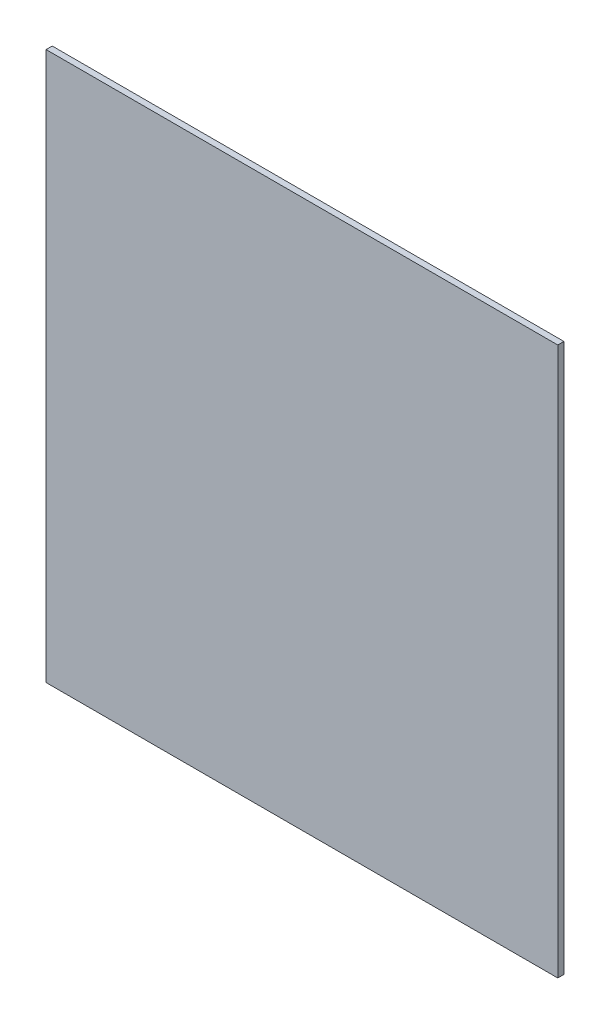
SolidWorks part; units mm, degrees
ref_plane "Front Plane" through (0, 0, 0) normal (0, 0, 1) x (1, 0, 0)
ref_plane "Top Plane" through (0, 0, 0) normal (0, 1, 0) x (1, 0, 0)
ref_plane "Right Plane" through (0, 0, 0) normal (1, 0, 0) x (0, 0, -1)
sketch "Sketch1" plane through (0, 0, 0) normal (0, 0, 1) x (1, 0, 0)
  line L0 (53.6, -267.4) -> (-17.4, -267.4) construction
  line L1 (0, 0) -> (249.6, 0)
  line L2 (0, 0) -> (0, -267.4)
  line L3 (0, -267.4) -> (249.6, -267.4)
  line L4 (249.6, 0) -> (249.6, -267.4)
  dimension "D2" = 249.6
extrude "Boss-Extrude1" add sketch "Sketch1" along normal blind 3
